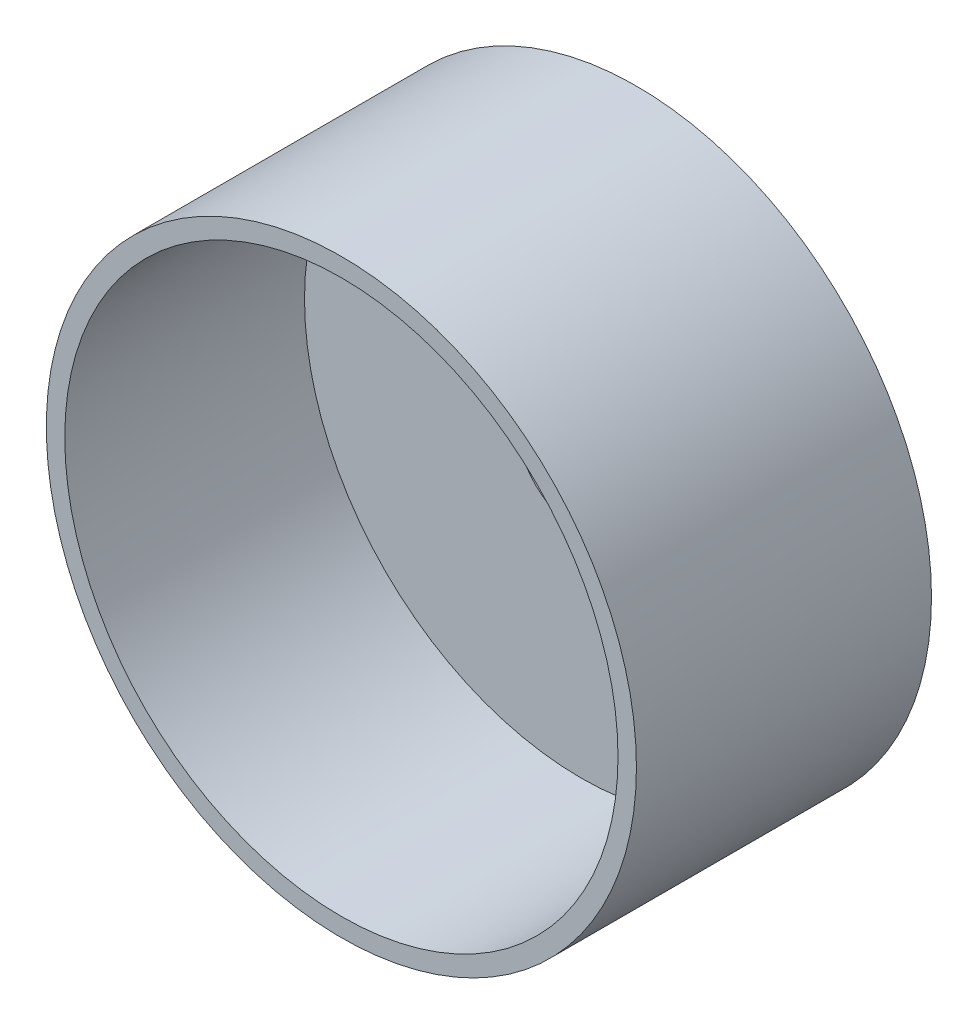
SolidWorks part; units mm, degrees
ref_plane "Front Plane" through (0, 0, 0) normal (0, 0, 1) x (1, 0, 0)
ref_plane "Top Plane" through (0, 0, 0) normal (0, 1, 0) x (1, 0, 0)
ref_plane "Right Plane" through (0, 0, 0) normal (1, 0, 0) x (0, 0, -1)
sketch "Sketch1" plane through (0, 0, 0) normal (0, 1, 0) x (1, 0, 0)
  line L0 (44.45, 0) -> (44.45, 44.45)
  line L1 (44.45, 44.45) -> (152.4, 44.45)
  line L2 (152.4, 44.45) -> (152.4, 38.1)
  line L3 (152.4, 38.1) -> (203.2, 38.1)
  line L4 (203.2, 38.1) -> (203.2, -165.1)
  line L5 (203.2, -165.1) -> (190.5, -165.1)
  line L6 (190.5, -165.1) -> (190.5, 0)
  line L7 (190.5, 0) -> (44.45, 0)
  line L8 (0, 0) -> (0, 44.45) construction
revolve "Revolve1" add sketch "Sketch1" angle 360 about L8
equation "\"A\"= 4"
equation "\"P_depth\"= 2 * \"A\""
equation "\"P_diam\"= 4 * \"A\""
equation "\"Mount_diam\"= 3 * \"A\""
equation "\"D3@Sketch1\"=\"Mount_diam\"/2"
equation "\"D4@Sketch1\"=\"P_diam\"/2"
equation "\"D5@Sketch1\"=\"P_depth\""
